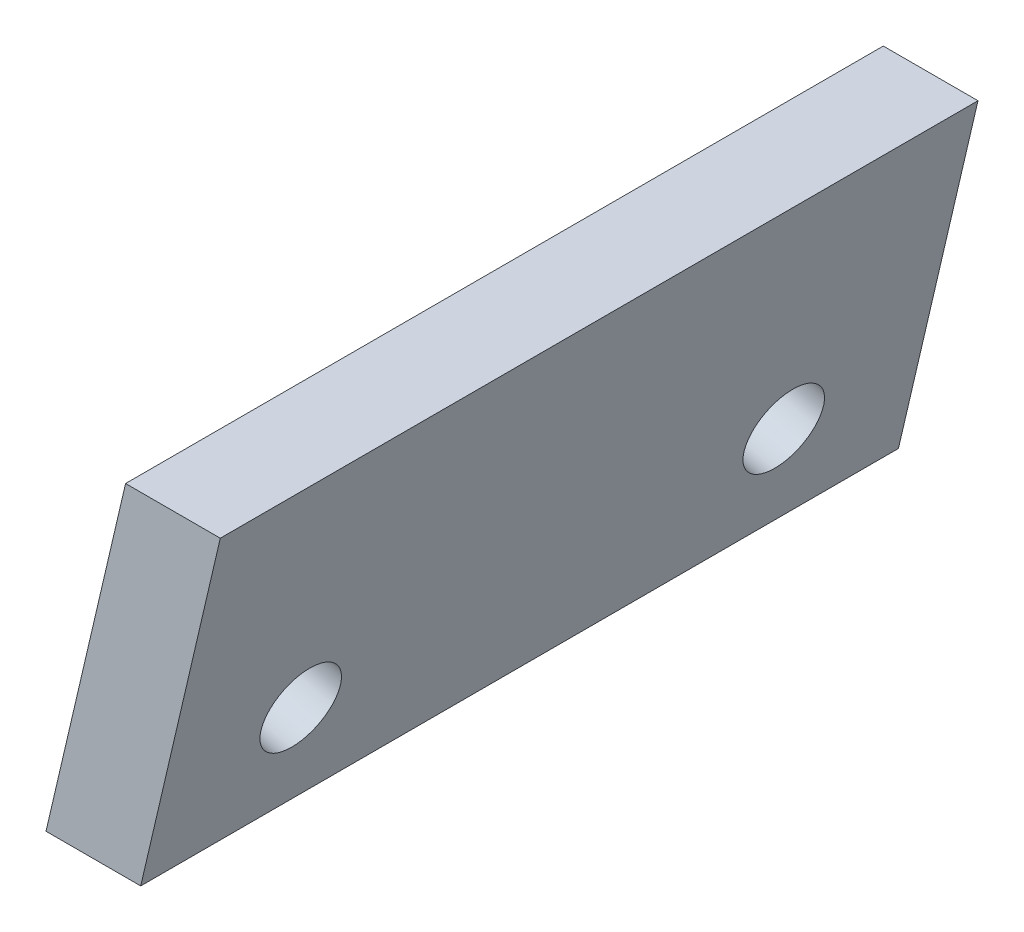
SolidWorks part; units mm, degrees
ref_plane "Front Plane" through (0, 0, 0) normal (0, 0, 1) x (1, 0, 0)
ref_plane "Top Plane" through (0, 0, 0) normal (0, 1, 0) x (1, 0, 0)
ref_plane "Right Plane" through (0, 0, 0) normal (1, 0, 0) x (0, 0, -1)
sketch "Sketch2" plane through (0, 0, 0) normal (0, 0, 1) x (1, 0, 0)
  line L0 (0, 0) -> (2.5, 0)
  line L1 (0, 0) -> (2.1002, 9)
  line L2 (2.5, 0) -> (4.6002, 9)
  line L3 (4.6002, 9) -> (2.1002, 9)
  dimension "D1" = 9
  dimension "D2" = 2.5
extrude "Boss-Extrude2" add sketch "Sketch2" along normal blind 20
sketch "Sketch4" plane through (0, 0, 0) normal (-0.9738, 0.2273, 0) x (0, 0, 1)
  line L1 (20, 9.2418) -> (20, 0) construction
  line L2 (20, 0) -> (0, 0) construction
  circle A0 centre (3.625, 3.2) radius 1.05
  circle A1 centre (16.375, 3.2) radius 1.05
  dimension "D1" = 12.75
  dimension "D2" = 3.625
  dimension "D3" = 3.2
  dimension "D4" = 3.2
  dimension "D5" = 2.1
  dimension "D6" = 2.1
extrude "Cut-Extrude1" cut sketch "Sketch4" against normal through all
